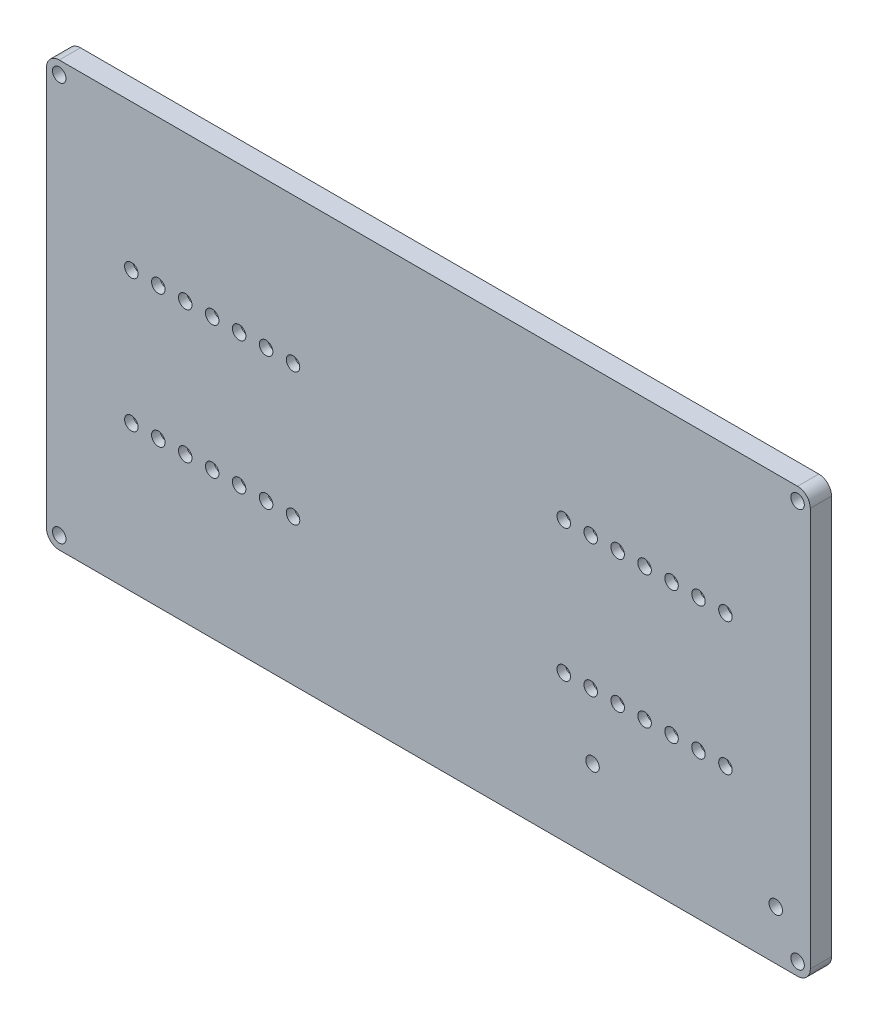
SolidWorks part; units mm, degrees
ref_plane "Front Plane" through (0, 0, 0) normal (0, 0, 1) x (1, 0, 0)
ref_plane "Top Plane" through (0, 0, 0) normal (0, 1, 0) x (1, 0, 0)
ref_plane "Right Plane" through (0, 0, 0) normal (1, 0, 0) x (0, 0, -1)
sketch "Sketch1" plane through (0, 0, 0) normal (0, 0, 1) x (1, 0, 0)
  line L0 (-90, 0) -> (90, 0) construction
  line L1 (-90, 50) -> (90, 50)
  line L2 (-90, 50) -> (-90, -50)
  line L3 (-90, -50) -> (90, -50)
  line L4 (90, 50) -> (90, -50)
  line L5 (-90, 50) -> (90, -50) construction
  line L6 (-90, -50) -> (90, 50) construction
  point P0 (0, 0)
  point P9 (0, 0)
  dimension "D1" = 100
  dimension "D2" = 180
extrude "Boss-Extrude1" add sketch "Sketch1" along normal blind 5 contours L1 L4 L3 L2
sketch "Sketch2" plane through (0, 0, 5) normal (0, 0, 1) x (1, 0, 0)
  line L0 (-90, 0) -> (90, 0) construction
  line L1 (-90, 50) -> (-90, -50) construction
  line L2 (90, 50) -> (90, -50) construction
  line L3 (0, 50) -> (0, -50) construction
  line L4 (-90, 50) -> (90, 50) construction
  line L5 (-90, -50) -> (90, -50) construction
  circle A0 centre (-70, 15.62) radius 1.59
  dimension "D1" = 3.18
  dimension "D2" = 70
  dimension "D3" = 15.62
extrude "Cut-Extrude1" cut sketch "Sketch2" against normal through all
pattern_linear "LPattern1" count 7 spacing 6.35 along (1, 0, 0) count 2 spacing 31.24 along (0, -1, 0) of "Cut-Extrude1"
ref_plane "Plane1" through (0, 0, 0) normal (1, 0, 0) x (0, 0, -1)
mirror "Mirror1" about plane through (0, 0, 0) normal (1, 0, 0) of "LPattern1", "Cut-Extrude1"
ref_plane "Plane2" through (0, 0, 0) normal (0, 1, 0) x (1, 0, 0)
sketch "Sketch4" plane through (0, 0, 0) normal (0, 0, -1) x (-1, 0, 0)
  line L0 (28.9, 15.62) -> (73, 15.62) construction
  line L1 (28.9, 18.22) -> (73, 18.22)
  line L2 (28.9, 18.22) -> (28.9, 13.02)
  line L3 (28.9, 13.02) -> (73, 13.02)
  line L4 (73, 18.22) -> (73, 13.02)
  circle A0 centre (70, 15.62) radius 1.59 construction
  circle A1 centre (70, 15.62) radius 1.59 construction
  circle A2 centre (31.9, 15.62) radius 1.59 construction
  circle A3 centre (31.9, 15.62) radius 1.59 construction
  dimension "D3" = 3
  dimension "D1" = 5.2
  dimension "D2" = 3
extrude "Cut-Extrude3" cut sketch "Sketch4" against normal blind 3
mirror "Mirror4" about plane through (0, 0, 0) normal (0, 1, 0) of "Cut-Extrude3"
mirror "Mirror5" about plane through (0, 0, 0) normal (1, 0, 0) of "Mirror4", "Cut-Extrude3"
fillet "Fillet1" radius 1 16 edges at (-28.9, -18.22, 1.5) (-28.9, -13.02, 1.5) (28.9, -13.02, 1.5) (73, -13.02, 1.5) (73, -18.22, 1.5) (28.9, -18.22, 1.5) (-73, -18.22, 1.5) (-73, -13.02, 1.5) (-73, 13.02, 1.5) (-73, 18.22, 1.5) (-28.9, 18.22, 1.5) (-28.9, 13.02, 1.5) (73, 13.02, 1.5) (73, 18.22, 1.5) (28.9, 13.02, 1.5) (28.9, 18.22, 1.5)
fillet "Fillet2" radius 3 4 edges at (90, -50, 2.5) (-90, -50, 2.5) (-90, 50, 2.5) (90, 50, 2.5)
sketch "Sketch5" plane through (0, 0, 0) normal (0, 0, -1) x (-1, 0, 0)
  line L1 (-81.8636, -38.3983) -> (-38.6836, -38.3983) construction
  line L2 (-81.8636, -38.3983) -> (-81.8636, -30.7783) construction
  line L3 (-81.8636, -30.7783) -> (-38.6836, -30.7783) construction
  line L4 (-38.6836, -38.3983) -> (-38.6836, -30.7783) construction
  circle A2 centre (-81.8636, -38.3983) radius 3
  circle A3 centre (-38.6836, -30.7783) radius 3
  dimension "D5" = 6
  dimension "D6" = 6
  dimension "D1" = 7.62
  dimension "D2" = 43.18
extrude "Boss-Extrude3" add sketch "Sketch5" along normal blind 3
sketch "Sketch11" plane through (0, 0, -3) normal (0, 0, -1) x (-1, 0, 0)
  circle A0 centre (-81.8636, -38.3983) radius 3 construction
  circle A1 centre (-81.8636, -38.3983) radius 3
  circle A2 centre (-81.8636, -38.3983) radius 1.59
  circle A3 centre (-38.6836, -30.7783) radius 1.59
  dimension "D1" = 3.18
  dimension "D2" = 3.18
extrude "Cut-Extrude5" cut sketch "Sketch11" against normal through all both and the other way through all contours A3 | A2
sketch "Sketch12" plane through (0, 0, 0) normal (0, 0, -1) x (-1, 0, 0)
  line L0 (-90, 47) -> (-90, -47) construction
  line L1 (-87, -47) -> (87, -47) construction
  line L2 (-87, -47) -> (-87, 47) construction
  line L3 (-87, 47) -> (87, 47) construction
  line L4 (87, -47) -> (87, 47) construction
  line L5 (87, 50) -> (-87, 50) construction
  line L6 (90, 47) -> (90, -47) construction
  line L7 (87, -50) -> (-87, -50) construction
  circle A0 centre (-87, -47) radius 1.59
  circle A1 centre (-87, 47) radius 1.59
  circle A2 centre (87, 47) radius 1.59
  circle A3 centre (87, -47) radius 1.59
  dimension "D1" = 3.18
  dimension "D2" = 3.18
  dimension "D3" = 3.18
  dimension "D4" = 3.18
  dimension "D5" = 3
  dimension "D6" = 3
  dimension "D7" = 3
  dimension "D8" = 3
extrude "Cut-Extrude6" cut sketch "Sketch12" against normal through all both and the other way through all
sketch "Sketch14" plane through (0, 0, 0) normal (0, 0, -1) x (-1, 0, 0)
  line L0 (-89, 45.3483) -> (-89, -45.3544)
  line L1 (-85.3544, -49) -> (85.3544, -49)
  line L2 (89, -45.3544) -> (89, 45.3544)
  line L3 (85.3544, 49) -> (-85.3483, 49)
  line L4 (-73, -14.02) -> (-73, -17.22) construction
  line L5 (73, -14.02) -> (73, -17.22) construction
  line L6 (-29.9, -13.02) -> (-72, -13.02) construction
  line L7 (-73, 14.02) -> (-73, 17.22) construction
  line L8 (-72, -18.22) -> (-29.9, -18.22) construction
  line L9 (-28.9, -17.22) -> (-28.9, -14.02) construction
  line L10 (-29.9, -12.02) -> (-72, -12.02)
  line L11 (29.9, -13.02) -> (72, -13.02) construction
  line L12 (72, -18.22) -> (29.9, -18.22) construction
  line L13 (28.9, -17.22) -> (28.9, -14.02) construction
  line L14 (73, 14.02) -> (73, 17.22) construction
  line L15 (-29.9, 13.02) -> (-72, 13.02) construction
  line L16 (-72, 18.22) -> (-29.9, 18.22) construction
  line L17 (-28.9, 17.22) -> (-28.9, 14.02) construction
  line L18 (-29.9, 13.02) -> (-72, 13.02) construction
  line L19 (-73, 14.02) -> (-73, 17.22) construction
  line L20 (-72, 18.22) -> (-29.9, 18.22) construction
  line L21 (74, -17.22) -> (74, -14.02)
  line L22 (-73, -14.02) -> (-73, -17.22) construction
  line L23 (-28.9, -17.22) -> (-28.9, -14.02) construction
  line L24 (-72, -18.22) -> (-29.9, -18.22) construction
  line L25 (-29.9, -13.02) -> (-72, -13.02) construction
  line L26 (29.9, 13.02) -> (72, 13.02) construction
  line L27 (28.9, 17.22) -> (28.9, 14.02) construction
  line L28 (72, 18.22) -> (29.9, 18.22) construction
  line L29 (73, -14.02) -> (73, -17.22) construction
  line L30 (29.9, -13.02) -> (72, -13.02) construction
  line L31 (72, -18.22) -> (29.9, -18.22) construction
  line L32 (28.9, -17.22) -> (28.9, -14.02) construction
  line L33 (73, 14.02) -> (73, 17.22) construction
  line L34 (29.9, 13.02) -> (72, 13.02) construction
  line L35 (28.9, 17.22) -> (28.9, 14.02) construction
  line L36 (72, 18.22) -> (29.9, 18.22) construction
  line L37 (72, -12.02) -> (29.9, -12.02)
  line L38 (27.9, -14.02) -> (27.9, -14.5041)
  line L39 (72, -19.22) -> (36.6294, -19.22)
  line L40 (74, 17.22) -> (74, 14.02)
  line L41 (72, 19.22) -> (36.6294, 19.22)
  line L42 (27.9, 17.22) -> (27.9, 15.6407)
  line L43 (29.9, 12.02) -> (72, 12.02)
  line L44 (-27.9, 14.02) -> (-27.9, 14.5041)
  line L45 (-29.9, 19.22) -> (-34.5255, 19.22)
  line L46 (-74, 17.22) -> (-74, 14.02)
  line L47 (-29.9, 12.02) -> (-72, 12.02)
  line L48 (-74, -14.02) -> (-74, -17.22)
  line L49 (-72, -19.22) -> (-36.6294, -19.22)
  line L50 (-27.9, -14.02) -> (-27.9, -14.5041)
  line L51 (-87, 47) -> (87, -47) construction
  line L52 (87, 47) -> (-87, -47) construction
  line L53 (0.0031, 49) -> (0, -49) construction
  line L54 (-85.0018, -45.3522) -> (-36.6294, -19.22)
  line L55 (-84.5265, -46.232) -> (-34.5255, -19.22)
  line L56 (-89, -0.0031) -> (89, 0) construction
  line L57 (34.5255, -19.22) -> (84.5265, -46.232)
  line L58 (85.0018, -45.3522) -> (36.6294, -19.22)
  line L59 (-84.523, 46.2301) -> (-34.5255, 19.22)
  line L60 (-84.9983, 45.3503) -> (-36.6294, 19.22)
  line L61 (34.5255, 19.22) -> (84.5265, 46.232)
  line L62 (36.6294, 19.22) -> (85.0018, 45.3522)
  line L63 (87, 50) -> (-87, 50) construction
  line L64 (-90, 47) -> (-90, -47) construction
  line L65 (90, 47) -> (90, -47) construction
  line L66 (87, -50) -> (-87, -50) construction
  line L67 (39.8193, 22.0799) -> (40.2946, 21.2001) construction
  line L68 (-51.9381, 27.4902) -> (-51.4628, 28.3701) construction
  line L69 (-56.6413, -30.031) -> (-56.166, -30.9109) construction
  line L70 (52.5149, -28.9384) -> (52.9902, -28.0586) construction
  line L71 (-34.5255, -19.22) -> (-29.9, -19.22)
  line L72 (-36.6294, 19.22) -> (-72, 19.22)
  line L73 (34.5255, 19.22) -> (29.9, 19.22)
  line L74 (34.5255, -19.22) -> (29.9, -19.22)
  line L75 (-27.9, 15.6407) -> (-0.7963, 0.9985)
  line L76 (27.9, -15.6407) -> (0.8019, -1.0015)
  line L77 (27.9, 15.6407) -> (0.7963, 0.9985)
  line L78 (27.9, 14.5041) -> (2.9003, 0.9985)
  line L79 (-21.5483, -11.0728) -> (-21.073, -11.9526) construction
  line L80 (8.7172, -5.2776) -> (9.1925, -4.3978) construction
  line L81 (-1.052, 0) -> (-1.0548, -0.0015)
  line L82 (1.052, 0) -> (1.0547, -0.0015)
  line L83 (0.0015, -0.5675) -> (0, -0.5683)
  line L84 (-1.0491, -0.0015) -> (-1.052, 0)
  line L85 (-27.9, 15.6407) -> (-27.9, 17.22)
  line L86 (27.9, 14.5041) -> (27.9, 14.02)
  line L87 (27.9, -15.6407) -> (27.9, -17.22)
  line L88 (-27.9, -15.6407) -> (-27.9, -17.22)
  line L89 (-89, 0.9969) -> (-2.9001, 0.9984)
  line L90 (89, -1) -> (2.9058, -1.0015)
  line L91 (-77.7041, 0.9971) -> (-77.7041, -1.0029) construction
  line L92 (-2.9001, 0.9984) -> (-27.9, 14.5041)
  line L93 (0, 0.5683) -> (0.0015, 0.5675)
  line L94 (0.0015, 0.5691) -> (0, 0.5683)
  line L95 (1.052, 0) -> (1.0492, -0.0015)
  line L96 (2.9058, -1.0015) -> (27.9, -14.5041)
  line L97 (0.0015, -0.5691) -> (0, -0.5683)
  line L98 (-0.802, -1.0015) -> (-27.9, -15.6407)
  line L99 (-2.9059, -1.0016) -> (-27.9, -14.5041)
  line L100 (-0.7963, 0.9985) -> (0.7963, 0.9985)
  line L101 (2.9003, 0.9985) -> (89, 1)
  line L102 (-2.9059, -1.0016) -> (-89, -1.0031)
  line L103 (0.8019, -1.0015) -> (-0.802, -1.0015)
  arc A0 (-89, -45.3544) -> (-85.3544, -49) centre (-87, -47) cw
  arc A1 (85.3544, -49) -> (89, -45.3544) centre (87, -47) cw
  arc A2 (85.3544, 49) -> (89, 45.3544) centre (87, 47) ccw
  arc A3 (-85.3483, 49) -> (-89, 45.3483) centre (-87, 47) cw
  arc A4 (72, -18.22) -> (73, -17.22) centre (72, -17.22) ccw construction
  arc A5 (73, -14.02) -> (72, -13.02) centre (72, -14.02) ccw construction
  arc A6 (28.9, -17.22) -> (29.9, -18.22) centre (29.9, -17.22) ccw construction
  arc A7 (29.9, -13.02) -> (28.9, -14.02) centre (29.9, -14.02) ccw construction
  arc A8 (73, 17.22) -> (72, 18.22) centre (72, 17.22) ccw construction
  arc A9 (72, 13.02) -> (73, 14.02) centre (72, 14.02) ccw construction
  arc A10 (28.9, 14.02) -> (29.9, 13.02) centre (29.9, 14.02) ccw construction
  arc A11 (29.9, 18.22) -> (28.9, 17.22) centre (29.9, 17.22) ccw construction
  arc A12 (72, -18.22) -> (73, -17.22) centre (72, -17.22) ccw construction
  arc A13 (73, -14.02) -> (72, -13.02) centre (72, -14.02) ccw construction
  arc A14 (28.9, -17.22) -> (29.9, -18.22) centre (29.9, -17.22) ccw construction
  arc A15 (29.9, -13.02) -> (28.9, -14.02) centre (29.9, -14.02) ccw construction
  arc A16 (73, 17.22) -> (72, 18.22) centre (72, 17.22) ccw construction
  arc A17 (72, 13.02) -> (73, 14.02) centre (72, 14.02) ccw construction
  arc A18 (28.9, 14.02) -> (29.9, 13.02) centre (29.9, 14.02) ccw construction
  arc A19 (29.9, 18.22) -> (28.9, 17.22) centre (29.9, 17.22) ccw construction
  arc A20 (-72, -13.02) -> (-73, -14.02) centre (-72, -14.02) ccw construction
  arc A21 (-73, -17.22) -> (-72, -18.22) centre (-72, -17.22) ccw construction
  arc A22 (-29.9, -18.22) -> (-28.9, -17.22) centre (-29.9, -17.22) ccw construction
  arc A23 (-28.9, -14.02) -> (-29.9, -13.02) centre (-29.9, -14.02) ccw construction
  arc A24 (-72, -13.02) -> (-73, -14.02) centre (-72, -14.02) ccw construction
  arc A25 (-73, -17.22) -> (-72, -18.22) centre (-72, -17.22) ccw construction
  arc A26 (-28.9, -14.02) -> (-29.9, -13.02) centre (-29.9, -14.02) ccw construction
  arc A27 (-29.9, -18.22) -> (-28.9, -17.22) centre (-29.9, -17.22) ccw construction
  arc A28 (-72, 18.22) -> (-73, 17.22) centre (-72, 17.22) ccw construction
  arc A29 (-28.9, 17.22) -> (-29.9, 18.22) centre (-29.9, 17.22) ccw construction
  arc A30 (-29.9, 13.02) -> (-28.9, 14.02) centre (-29.9, 14.02) ccw construction
  arc A31 (-73, 14.02) -> (-72, 13.02) centre (-72, 14.02) ccw construction
  arc A32 (-28.9, 17.22) -> (-29.9, 18.22) centre (-29.9, 17.22) ccw construction
  arc A33 (-29.9, 13.02) -> (-28.9, 14.02) centre (-29.9, 14.02) ccw construction
  arc A34 (-73, 14.02) -> (-72, 13.02) centre (-72, 14.02) ccw construction
  arc A35 (-72, 18.22) -> (-73, 17.22) centre (-72, 17.22) ccw construction
  arc A36 (-74, 17.22) -> (-72, 19.22) centre (-72, 17.22) cw
  arc A37 (-29.9, 19.22) -> (-27.9, 17.22) centre (-29.9, 17.22) cw
  arc A38 (-27.9, 14.02) -> (-29.9, 12.02) centre (-29.9, 14.02) cw
  arc A39 (-72, 12.02) -> (-74, 14.02) centre (-72, 14.02) cw
  arc A40 (-27.9, -17.22) -> (-29.9, -19.22) centre (-29.9, -17.22) cw
  arc A41 (-27.9, -14.02) -> (-29.9, -12.02) centre (-29.9, -14.02) ccw
  arc A42 (-72, -12.02) -> (-74, -14.02) centre (-72, -14.02) ccw
  arc A43 (-72, -19.22) -> (-74, -17.22) centre (-72, -17.22) cw
  arc A44 (29.9, -19.22) -> (27.9, -17.22) centre (29.9, -17.22) cw
  arc A45 (27.9, -14.02) -> (29.9, -12.02) centre (29.9, -14.02) cw
  arc A46 (74, 17.22) -> (72, 19.22) centre (72, 17.22) ccw
  arc A47 (72, 12.02) -> (74, 14.02) centre (72, 14.02) ccw
  arc A48 (29.9, 19.22) -> (27.9, 17.22) centre (29.9, 17.22) ccw
  arc A49 (27.9, 14.02) -> (29.9, 12.02) centre (29.9, 14.02) ccw
  arc A50 (72, -12.02) -> (74, -14.02) centre (72, -14.02) cw
  arc A51 (74, -17.22) -> (72, -19.22) centre (72, -17.22) cw
  circle A52 centre (-87, 47) radius 1.59 construction
  circle A53 centre (87, 47) radius 1.59 construction
  circle A54 centre (87, -47) radius 1.59 construction
  circle A55 centre (-87, -47) radius 1.59 construction
  point P135 (-51.7005, 27.9302)
  point P139 (-56.4037, -30.471)
  point P141 (52.7526, -28.4985)
  point P146 (40.057, 21.64)
  point P155 (-21.3107, -11.5127)
  point P159 (8.9549, -4.8377)
  point P170 (1.0492, 0)
  point P173 (-77.7041, -0.0029)
  point P186 (0, 0)
  point P189 (-1.1254, 31.1591)
  dimension "D3" = 1.0039
  dimension "D7" = 1
  dimension "D8" = 1
  dimension "D11" = 1
  dimension "D15" = 1
  dimension "D1" = 1
  dimension "D2" = 1
  dimension "D4" = 1
  dimension "D5" = 1
  dimension "D6" = 1
  dimension "D9" = 1
  dimension "D10" = 1
  dimension "D12" = 1
  dimension "D13" = 1
  dimension "D14" = 1
  dimension "D16" = 1
  dimension "D17" = 1
  dimension "D18" = 1
  dimension "D19" = 2
extrude "Cut-Extrude7" cut sketch "Sketch14" against normal blind 4
